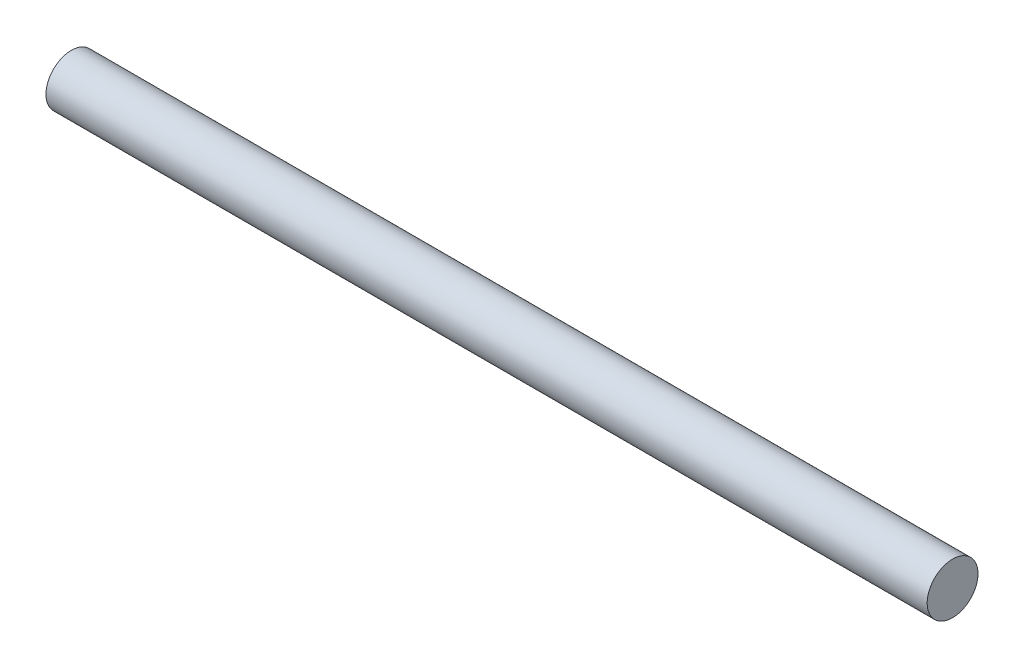
SolidWorks part; units mm, degrees
ref_plane "Front Plane" through (0, 0, 0) normal (0, 0, 1) x (1, 0, 0)
ref_plane "Top Plane" through (0, 0, 0) normal (0, 1, 0) x (1, 0, 0)
ref_plane "Right Plane" through (0, 0, 0) normal (1, 0, 0) x (0, 0, -1)
sketch "Sketch1" plane through (0, 0, 0) normal (1, 0, 0) x (0, 0, -1)
  circle A0 centre (-22.6945, 11.063) radius 0.75
  dimension "D1" = 1.5
extrude "Boss-Extrude1" add sketch "Sketch1" along normal blind 26
